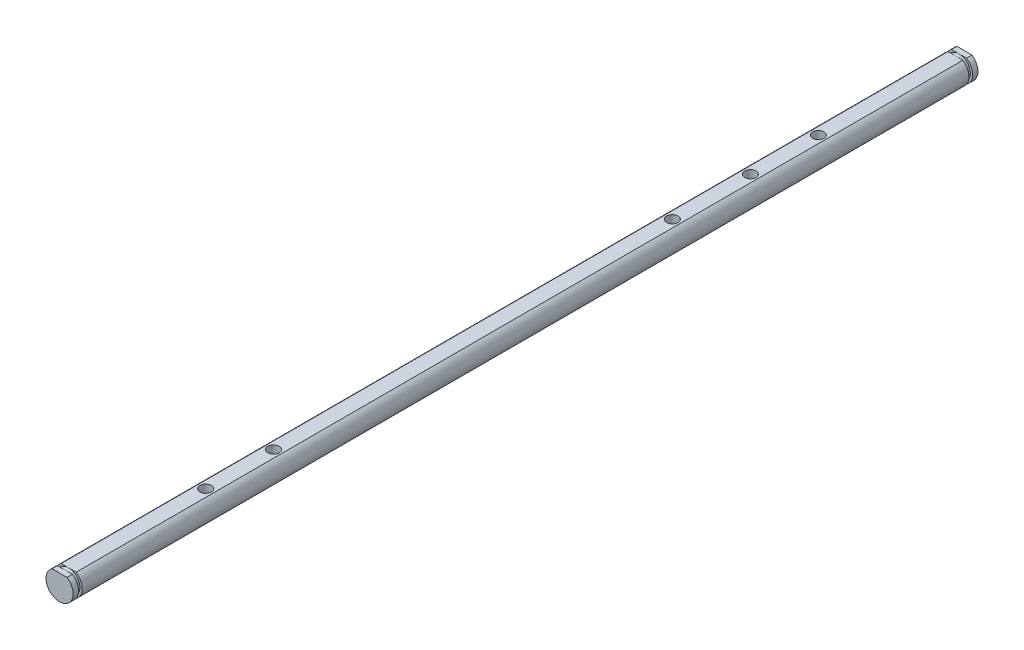
SolidWorks part; units mm, degrees
ref_plane "Front" through (0, 0, 0) normal (0, 0, 1) x (1, 0, 0)
ref_plane "Top" through (0, 0, 0) normal (0, 1, 0) x (1, 0, 0)
ref_plane "Right" through (0, 0, 0) normal (1, 0, 0) x (0, 0, -1)
sketch "Sketch1" plane through (0, 0, 0) normal (0, 0, 1) x (1, 0, 0)
  circle A0 centre (0, 0) radius 3
  dimension "D1" = 6
extrude "Boss-Extrude1" add sketch "Sketch1" along normal blind 200
sketch "Sketch2" plane through (0, 0, 200) normal (0, 0, 1) x (1, 0, 0)
  line L0 (-1.6583, 2.5) -> (1.6583, 2.5)
  line L1 (0, 2.5) -> (0, -3) construction
  circle A0 centre (0, 0) radius 3 construction
  circle A1 centre (0, 0) radius 3
  arc A2 (1.6583, 2.5) -> (-1.6583, 2.5) centre (0, 0) ccw
  dimension "D2" = 5.5
  dimension "D1" = 0
extrude "Cut-Extrude1" cut sketch "Sketch2" against normal through all
sketch "Sketch5" plane through (0, 2.5, 0) normal (0, 1, 0) x (1, 0, 0)
  circle A0 centre (0, -167.7) radius 1.5
  circle A1 centre (0, -152.7) radius 1.5
  circle A2 centre (0, -47.3) radius 1.5
  circle A3 centre (0, -32.3) radius 1.5
  dimension "D1" = 3
hole_wizard "M3 Tapped Hole1" positions "3DSketch3" profile "Sketch6" tap size "M3" standard "ISO" end condition through all
sketch3d "3DSketch3"
  point P0 (0, 2.5, 167.7)
  point P3 (0, 2.5, 152.7)
  point P6 (0, 2.5, 47.3)
  point P9 (0, 2.5, 32.3)
sketch "Sketch6" plane through (0, 2.5, 167.7) normal (1, 0, 0) x (0, 0, 1)
  line L0 (0, 0) -> (0, 5.5)
  line L1 (0, 5.5) -> (1.25, 5.5)
  line L2 (1.25, 5.5) -> (1.25, 0)
  line L5 (1.25, 0) -> (0, 0)
  line L11 (0, -6.35) -> (0, 107.95) construction
  dimension "Thru Tap Drill Dia." = 2.5
  dimension "Thru Tap Drill Depth" = 5.5
cosmetic thread "Hole Thread6" parameters "D1"=0, "D2"=3.5
cosmetic thread "Hole Thread7" parameters "D1"=0, "D2"=3.5
cosmetic thread "Hole Thread8" parameters "D1"=0, "D2"=3.5
cosmetic thread "Hole Thread9" parameters "D1"=0, "D2"=3.5
sketch "Sketch7" plane through (0, 2.5, 0) normal (0, 1, 0) x (1, 0, 0)
  circle A0 centre (0, -64.5488) radius 1.5
  dimension "D1" = 3
hole_wizard "M3 Tapped Hole2" positions "3DSketch4" profile "Sketch8" tap size "M3" standard "ISO" end condition through all
sketch3d "3DSketch4"
  point P0 (0, 2.5, 64.5488)
sketch "Sketch8" plane through (0, 2.5, 64.5488) normal (1, 0, 0) x (0, 0, 1)
  line L0 (0, 0) -> (0, 5.5)
  line L1 (0, 5.5) -> (1.25, 5.5)
  line L2 (1.25, 5.5) -> (1.25, 0)
  line L5 (1.25, 0) -> (0, 0)
  line L11 (0, -6.35) -> (0, 107.95) construction
  dimension "Thru Tap Drill Dia." = 2.5
  dimension "Thru Tap Drill Depth" = 5.5
cosmetic thread "Hole Thread10" parameters "D1"=0, "D2"=3.5
sketch "Sketch9" plane through (0, 0, 200) normal (0, 0, 1) x (1, 0, 0)
  circle A0 centre (0, 0) radius 2.5
  circle A1 centre (0, 0) radius 3
  arc A2 (-1.6583, 2.5) -> (1.6583, 2.5) centre (0, 0) ccw construction
  dimension "D1" = 0.5
extrude "Cut-Extrude2" cut sketch "Sketch9" against normal blind 0.8 from offset 1.2 offset against normal yes
ref_plane "Plane3" through (0, 0, 100) normal (0, 0, 1) x (1, 0, 0)
mirror "Mirror1" about plane through (0, 0, 100) normal (0, 0, 1) of "Cut-Extrude2"
